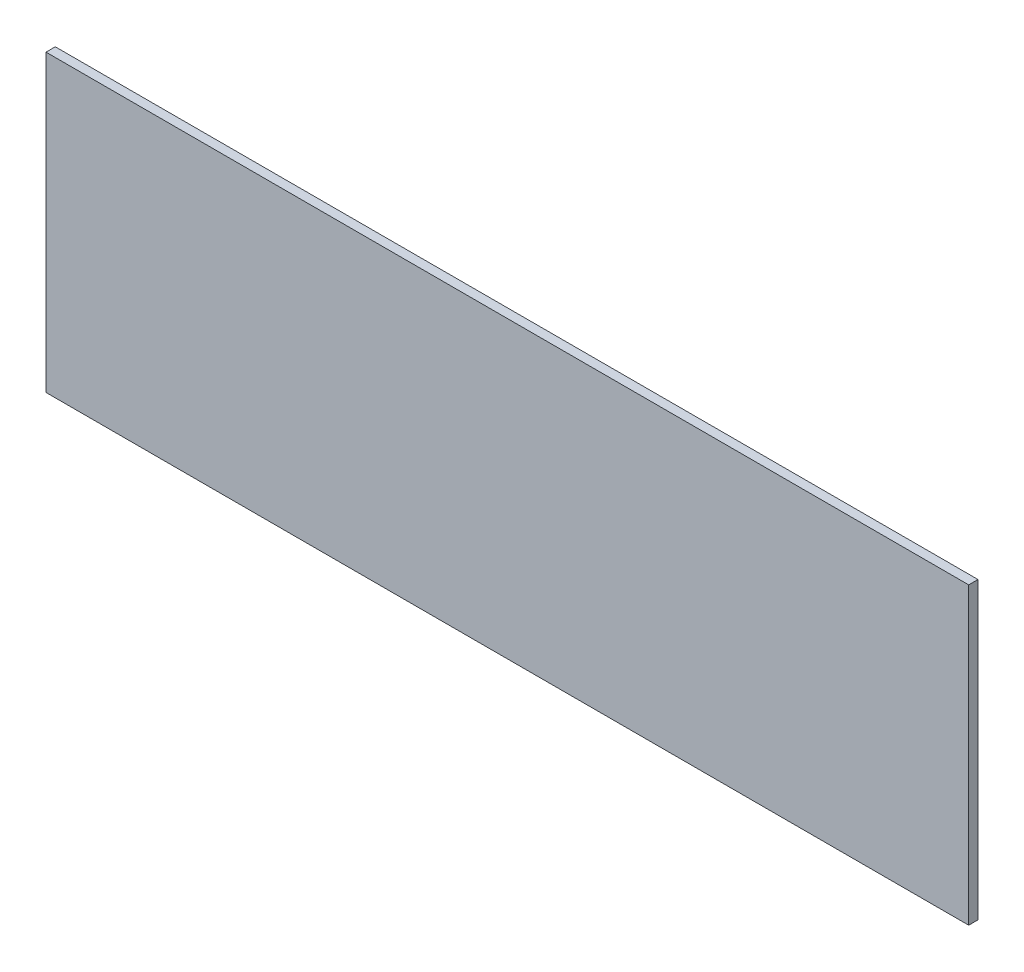
SolidWorks part; units mm, degrees
ref_plane "Front Plane" through (0, 0, 0) normal (0, 0, 1) x (1, 0, 0)
ref_plane "Top Plane" through (0, 0, 0) normal (0, 1, 0) x (1, 0, 0)
ref_plane "Right Plane" through (0, 0, 0) normal (1, 0, 0) x (0, 0, -1)
sketch "Sketch1" plane through (0, 0, 0) normal (0, 0, 1) x (1, 0, 0)
  line L0 (-148.082, 34.29) -> (150.078, 34.29)
  line L1 (150.078, -60.96) -> (-148.082, -60.96)
  line L2 (150.078, -60.96) -> (150.078, 34.29)
  line L4 (-148.082, -60.96) -> (-148.082, 34.29)
  point P0 (0, 0)
  dimension "D1" = 298.16
  dimension "D3" = 95.25
extrude "Boss-Extrude1" add sketch "Sketch1" along normal blind 3 contours L2 L0 L4 L1
